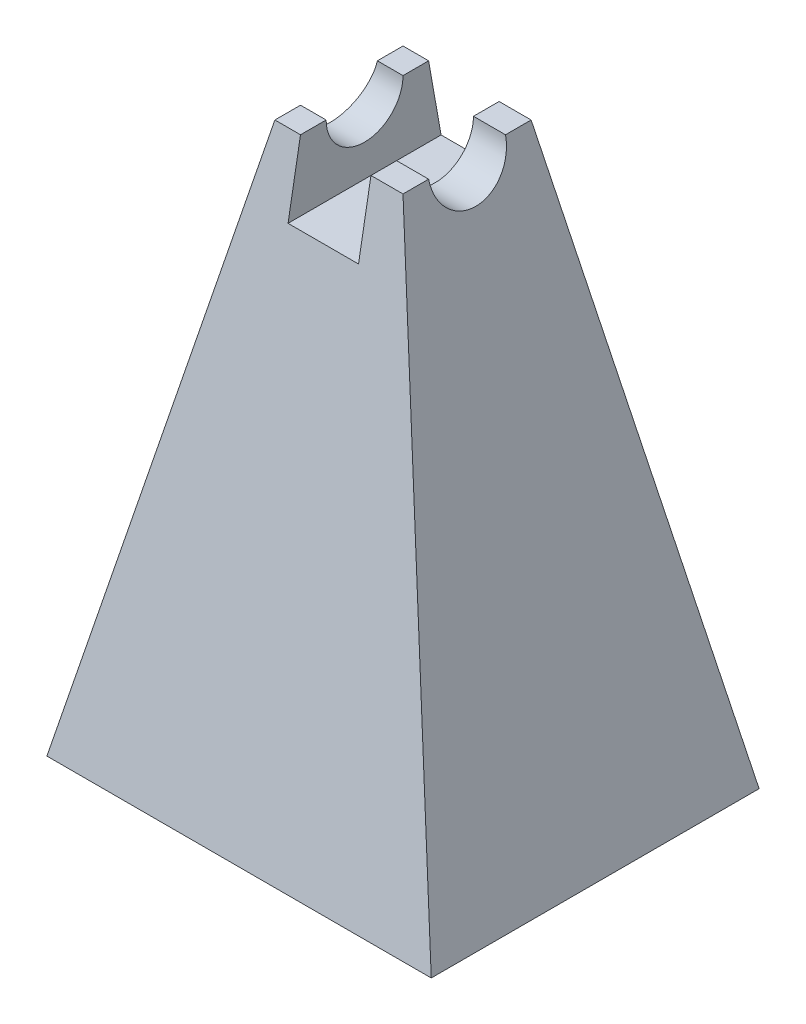
SolidWorks part; units mm, degrees
material "1.0035 (S185)"
ref_plane "Front Plane" through (0, 0, 0) normal (0, 0, 1) x (1, 0, 0)
ref_plane "Top Plane" through (0, 0, 0) normal (0, 1, 0) x (1, 0, 0)
ref_plane "Right Plane" through (0, 0, 0) normal (1, 0, 0) x (0, 0, -1)
sketch "Sketch2" plane through (0, 0, 0) normal (0, 0, 1) x (1, 0, 0)
  line L0 (-38.1, -56.007) -> (-12.7, 56.007)
  line L1 (-12.7, 56.007) -> (12.7, 56.007)
  line L2 (12.7, 56.007) -> (38.1, -56.007)
  line L3 (38.1, -56.007) -> (-38.1, -56.007)
  point P2 (0, 56.007)
  point P5 (0, -56.007)
  point P7 (0, 0)
  dimension "D1" = 112.014
  dimension "D2" = 56.007
  dimension "D3" = 76.2
  dimension "D4" = 25.4
extrude "Boss-Extrude1" add sketch "Sketch2" against normal blind 65
sketch "Sketch3" plane through (0, 0, 0) normal (1, 0, 0) x (0, 0, -1)
  line L0 (0, -56.007) -> (19.8, 56.007)
  line L1 (65, 56.007) -> (0, 56.007) construction
  line L2 (19.8, 56.007) -> (0, 56.007)
  line L3 (0, 56.007) -> (0, -56.007)
  line L4 (65, -56.007) -> (45.2, 56.007)
  line L5 (45.2, 56.007) -> (65, 56.007)
  line L6 (65, 56.007) -> (65, -56.007)
  dimension "D1" = 25.4
  dimension "D2" = 19.8
extrude "Cut-Extrude1" cut sketch "Sketch3" against normal through all both and the other way through all
sketch "Sketch4" plane through (0, 0, 0) normal (0, 0, 1) x (1, 0, 0)
  line L0 (-7.62, 56.007) -> (-7.62, 42.037)
  line L1 (-12.7, 56.007) -> (12.7, 56.007) construction
  line L2 (-7.62, 42.037) -> (6.35, 42.037)
  line L3 (6.35, 42.037) -> (6.35, 56.007)
  line L4 (6.35, 56.007) -> (-7.62, 56.007)
  dimension "D1" = 13.97
  dimension "D2" = 6.35
  dimension "D3" = 13.97
extrude "Cut-Extrude2" cut sketch "Sketch4" against normal through all both and the other way through all
sketch "Sketch5" plane through (0, 0, 0) normal (1, 0, 0) x (0, 0, -1)
  line L0 (45.2, 56.007) -> (19.8, 56.007) construction
  line L1 (40.12, 56.007) -> (24.88, 56.007)
  arc A0 (40.12, 56.007) -> (24.88, 56.007) centre (32.5, 56.007) cw
  dimension "0.3" = 7.62
extrude "Cut-Extrude4" cut sketch "Sketch5" against normal through all both and the other way through all
equation "\"D2@Sketch2\"=\"D1@Sketch2\"/2"
